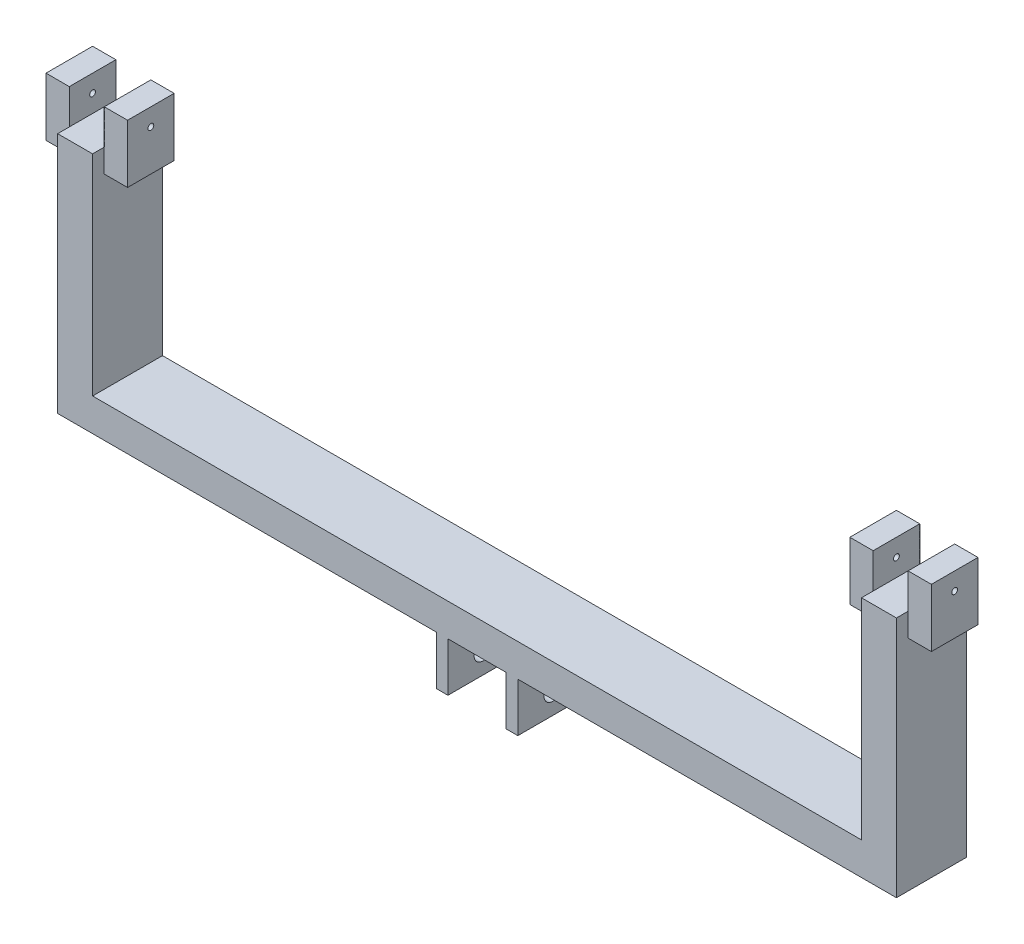
SolidWorks part; units mm, degrees
ref_plane "Front Plane" through (0, 0, 0) normal (0, 0, 1) x (1, 0, 0)
ref_plane "Top Plane" through (0, 0, 0) normal (0, 1, 0) x (1, 0, 0)
ref_plane "Right Plane" through (0, 0, 0) normal (1, 0, 0) x (0, 0, -1)
sketch "Sketch1" plane through (0, 0, 0) normal (0, 0, 1) x (1, 0, 0)
  line L1 (0, 0) -> (177.8, 0)
  line L2 (0, 0) -> (0, 177.8)
  line L3 (0, 177.8) -> (177.8, 177.8)
  line L4 (177.8, 0) -> (177.8, 177.8)
  dimension "D1" = 177.8
  dimension "D2" = 177.8
extrude "Boss-Extrude1" add sketch "Sketch1" along normal blind 152.4
sketch "Sketch2" plane through (0, 0, 152.4) normal (0, 0, 1) x (1, 0, 0)
  line L0 (0, 0) -> (177.8, 0) construction
  line L1 (25.4, 0) -> (152.4, 0)
  line L2 (25.4, 0) -> (25.4, 106.68)
  line L3 (25.4, 106.68) -> (152.4, 106.68)
  line L4 (152.4, 0) -> (152.4, 106.68)
  line L5 (0, 177.8) -> (0, 0) construction
  line L6 (177.8, 0) -> (177.8, 177.8) construction
  dimension "D1" = 25.4
  dimension "D2" = 25.4
  dimension "D3" = 106.68
extrude "Cut-Extrude1" cut sketch "Sketch2" against normal blind 152.4
sketch "Sketch3" plane through (177.8, 0, 0) normal (1, 0, 0) x (0, 0, -1)
  line L0 (-152.4, 0) -> (0, 0) construction
  line L1 (-152.4, 0) -> (-152.4, 177.8) construction
  circle A0 centre (-76.2, 45.72) radius 19.05
  point P2 (-76.2, 0)
  dimension "D1" = 38.1
  dimension "D2" = 45.72
  dimension "D3" = 76.2
extrude "Cut-Extrude2" cut sketch "Sketch3" against normal blind 182.626
sketch "Sketch4" plane through (177.8, 0, 0) normal (1, 0, 0) x (0, 0, -1)
  line L0 (-152.4, 0) -> (-152.4, 177.8) construction
  line L1 (0, 177.8) -> (-152.4, 177.8)
  line L2 (0, 177.8) -> (0, 106.68)
  line L3 (0, 106.68) -> (-152.4, 106.68)
  line L4 (-152.4, 177.8) -> (-152.4, 106.68)
  dimension "D1" = 71.12
extrude "Boss-Extrude2" add sketch "Sketch4" along normal blind 825.5
sketch "Sketch5" plane through (0, 0, 0) normal (-1, 0, 0) x (0, 0, 1)
  line L0 (152.4, 177.8) -> (152.4, 0) construction
  line L1 (0, 177.8) -> (152.4, 177.8)
  line L2 (0, 177.8) -> (0, 106.68)
  line L3 (0, 106.68) -> (152.4, 106.68)
  line L4 (152.4, 177.8) -> (152.4, 106.68)
  dimension "D1" = 71.12
extrude "Boss-Extrude3" add sketch "Sketch5" along normal blind 825.5
sketch "Sketch6" plane through (0, 177.8, 0) normal (0, 1, 0) x (1, 0, 0)
  line L0 (1003.3, -152.4) -> (-825.5, -152.4) construction
  line L1 (-825.5, 0) -> (-749.3, 0)
  line L2 (-825.5, 0) -> (-825.5, -152.4)
  line L3 (-825.5, -152.4) -> (-749.3, -152.4)
  line L4 (-749.3, 0) -> (-749.3, -152.4)
  line L6 (1003.3, 0) -> (927.1, 0)
  line L7 (1003.3, 0) -> (1003.3, -152.4)
  line L8 (1003.3, -152.4) -> (927.1, -152.4)
  line L9 (927.1, 0) -> (927.1, -152.4)
  dimension "D1" = 76.2
  dimension "D2" = 76.2
extrude "Boss-Extrude4" add sketch "Sketch6" along normal blind 457.2
sketch "Sketch7" plane through (-825.5, 0, 0) normal (-1, 0, 0) x (0, 0, 1)
  line L0 (0, 635) -> (152.4, 635) construction
  line L1 (25.4, 635) -> (127, 635)
  line L2 (25.4, 635) -> (25.4, 584.2)
  line L3 (25.4, 584.2) -> (127, 584.2)
  line L4 (127, 635) -> (127, 584.2)
  line L5 (0, 635) -> (0, 106.68) construction
  line L6 (152.4, 106.68) -> (152.4, 635) construction
  dimension "D1" = 25.4
  dimension "D2" = 25.4
  dimension "D3" = 50.8
extrude "Boss-Extrude9" add sketch "Sketch7" along normal blind 50.8
sketch "Sketch12" plane through (-749.3, 0, 0) normal (1, 0, 0) x (0, 0, -1)
  line L0 (0, 106.68) -> (0, 635) construction
  line L1 (-127, 635) -> (-25.4, 635)
  line L2 (-127, 635) -> (-127, 584.2)
  line L3 (-127, 584.2) -> (-25.4, 584.2)
  line L4 (-25.4, 635) -> (-25.4, 584.2)
  dimension "D1" = 50.8
  dimension "D2" = 25.4
extrude "Boss-Extrude10" add sketch "Sketch12" along normal blind 50.8
sketch "Sketch13" plane through (927.1, 0, 0) normal (-1, 0, 0) x (0, 0, 1)
  line L1 (25.4, 635) -> (127, 635)
  line L2 (25.4, 635) -> (25.4, 584.2)
  line L3 (25.4, 584.2) -> (127, 584.2)
  line L4 (127, 635) -> (127, 584.2)
extrude "Boss-Extrude11" add sketch "Sketch13" along normal blind 50.8
sketch "Sketch14" plane through (1003.3, 0, 0) normal (1, 0, 0) x (0, 0, -1)
  line L0 (0, 106.68) -> (0, 635) construction
  line L1 (-127, 635) -> (-25.4, 635)
  line L2 (-127, 635) -> (-127, 584.2)
  line L3 (-127, 584.2) -> (-25.4, 584.2)
  line L4 (-25.4, 635) -> (-25.4, 584.2)
  dimension "D1" = 50.8
  dimension "D2" = 25.4
extrude "Boss-Extrude12" add sketch "Sketch14" along normal blind 50.8
sketch "Sketch15" plane through (0, 635, 0) normal (0, 1, 0) x (1, 0, 0)
  line L1 (876.3, -25.4) -> (927.1, -25.4)
  line L2 (876.3, -25.4) -> (876.3, -127)
  line L3 (876.3, -127) -> (927.1, -127)
  line L4 (927.1, -25.4) -> (927.1, -127)
  line L5 (1003.3, -25.4) -> (1054.1, -25.4)
  line L6 (1003.3, -25.4) -> (1003.3, -127)
  line L7 (1003.3, -127) -> (1054.1, -127)
  line L8 (1054.1, -25.4) -> (1054.1, -127)
extrude "Boss-Extrude13" add sketch "Sketch15" along normal blind 76.2
sketch "Sketch16" plane through (0, 635, 0) normal (0, 1, 0) x (1, 0, 0)
  line L1 (-749.3, -25.4) -> (-698.5, -25.4)
  line L2 (-749.3, -25.4) -> (-749.3, -127)
  line L3 (-749.3, -127) -> (-698.5, -127)
  line L4 (-698.5, -25.4) -> (-698.5, -127)
  line L5 (-876.3, -25.4) -> (-825.5, -25.4)
  line L6 (-876.3, -25.4) -> (-876.3, -127)
  line L7 (-876.3, -127) -> (-825.5, -127)
  line L8 (-825.5, -25.4) -> (-825.5, -127)
extrude "Boss-Extrude14" add sketch "Sketch16" along normal blind 76.2
sketch "Sketch17" plane through (-876.3, 0, 0) normal (-1, 0, 0) x (0, 0, 1)
  line L0 (127, 584.2) -> (127, 711.2) construction
  line L1 (127, 711.2) -> (25.4, 711.2) construction
  circle A0 centre (76.2, 673.1) radius 6.35
  point P4 (76.2, 711.2)
  dimension "D1" = 12.7
  dimension "D2" = 50.8
  dimension "D3" = 38.1
extrude "Cut-Extrude3" cut sketch "Sketch17" against normal blind 205.994
sketch "Sketch18" plane through (1054.1, 0, 0) normal (1, 0, 0) x (0, 0, -1)
  line L0 (-25.4, 584.2) -> (-25.4, 711.2) construction
  line L1 (-127, 711.2) -> (-25.4, 711.2) construction
  circle A0 centre (-76.2, 673.1) radius 6.35
  dimension "D1" = 12.7
  dimension "D2" = 50.8
  dimension "D3" = 38.1
extrude "Cut-Extrude4" cut sketch "Sketch18" against normal blind 205.994
